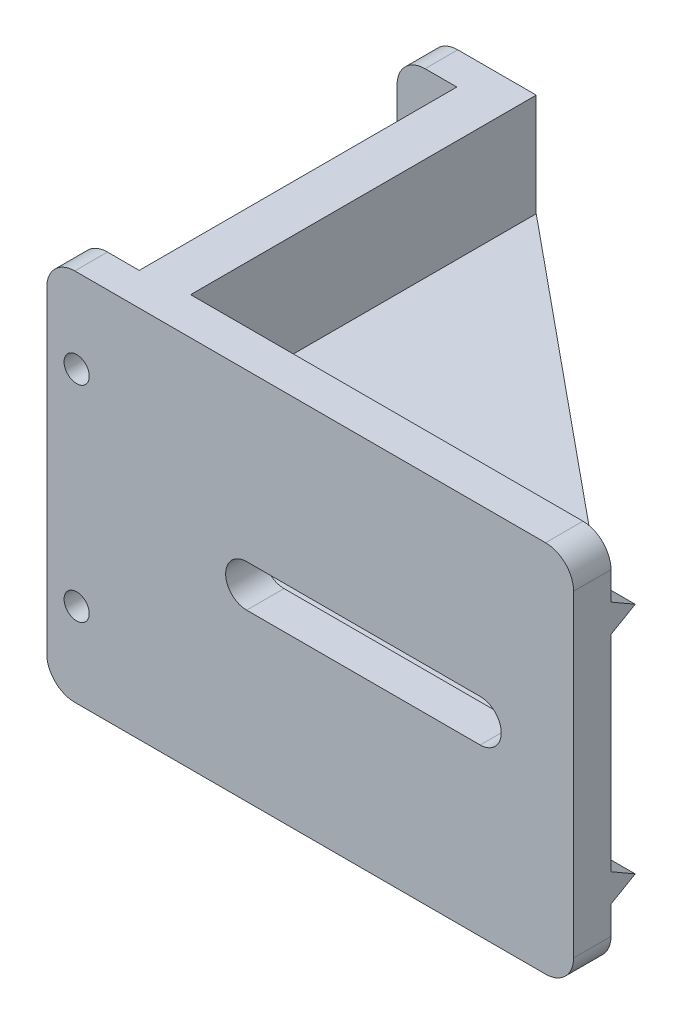
SolidWorks part; units mm, degrees
ref_plane "정면" through (0, 0, 0) normal (0, 0, 1) x (1, 0, 0)
ref_plane "윗면" through (0, 0, 0) normal (0, 1, 0) x (1, 0, 0)
ref_plane "우측면" through (0, 0, 0) normal (1, 0, 0) x (0, 0, -1)
sketch "스케치1" plane through (0, 0, 0) normal (1, 0, 0) x (0, 0, -1)
  line L1 (0, 0) -> (41, 0)
  line L2 (0, 0) -> (0, 40)
  line L3 (0, 40) -> (41, 40)
  line L4 (41, 0) -> (41, 40)
  dimension "D1" = 41
  dimension "D2" = 40
extrude "보스-돌출1" add sketch "스케치1" along normal blind 5
sketch "스케치2" plane through (0, 0, 0) normal (-1, 0, 0) x (0, 0, 1)
  line L0 (-41, 40) -> (0, 40) construction
  line L1 (-3.5, 40) -> (0, 40)
  line L2 (-3.5, 40) -> (-3.5, 0)
  line L3 (-3.5, 0) -> (0, 0)
  line L4 (0, 40) -> (0, 0)
  line L5 (-20.5, -5.7366) -> (-20.5, 42.7612) construction
  line L6 (-37.5, 0) -> (-41, 0)
  line L7 (-41, 40) -> (-41, 0)
  line L8 (-37.5, 40) -> (-41, 40)
  line L9 (-37.5, 40) -> (-37.5, 0)
  dimension "D1" = 3.5
extrude "보스-돌출2" add sketch "스케치2" along normal blind 6.4
sketch "스케치3" plane through (5, 0, 0) normal (1, 0, 0) x (0, 0, -1)
  line L0 (0, 0) -> (41, 0) construction
  line L1 (0, 40) -> (4, 40)
  line L2 (0, 40) -> (0, 0)
  line L3 (0, 0) -> (4, 0)
  line L4 (4, 40) -> (4, 34)
  line L5 (4, 34) -> (6.5981, 32.5)
  line L6 (4, 31) -> (6.5981, 32.5)
  line L7 (-6.5126, 20) -> (43.5218, 20) construction
  line L10 (4, 31) -> (4, 14)
  line L11 (4, 12) -> (4, 9)
  line L12 (4, 14) -> (4, 12)
  line L13 (4, 9) -> (6.5981, 7.5)
  line L14 (4, 6) -> (6.5981, 7.5)
  line L15 (4, 6) -> (4, 0)
  dimension "D1" = 4
  dimension "D2" = 6
  dimension "D3" = 60
  dimension "D4" = 60
  dimension "D5" = 3
  dimension "D6" = 40
extrude "보스-돌출3" add sketch "스케치3" along normal blind 45
sketch "스케치4" plane through (0, 0, -4) normal (0, 0, -1) x (-1, 0, 0)
  line L0 (-50, 9) -> (-50, 31) construction
  line L1 (-50, 29) -> (-5, 29)
  line L2 (-50, 29) -> (-50, 25)
  line L3 (-50, 25) -> (-5, 25)
  line L4 (-5, 29) -> (-5, 25)
  line L5 (-5, 9) -> (-5, 31) construction
  line L8 (-50, 40) -> (-5, 40) construction
  line L10 (-55.9639, 20) -> (9.4654, 20) construction
  line L11 (-50, 15) -> (-5, 15)
  line L12 (-5, 11) -> (-5, 15)
  line L13 (-50, 11) -> (-5, 11)
  line L14 (-50, 11) -> (-50, 15)
  dimension "D1" = 4
  dimension "D2" = 11
extrude "보스-돌출4" add sketch "스케치4" along normal blind 37
sketch "스케치5" plane through (0, 29, 0) normal (0, 1, 0) x (1, 0, 0)
  line L0 (50, 4) -> (5, 41)
  line L1 (5, 41) -> (50, 41)
  line L2 (50, 41) -> (50, 4)
extrude "컷-돌출1" cut sketch "스케치5" against normal blind 19
sketch "스케치6" plane through (0, 0, -41) normal (0, 0, -1) x (-1, 0, 0)
  line L2 (-5, 0) -> (6.4, 0) construction
  line L3 (6.4, 40) -> (6.4, 0) construction
  line L4 (-5, 40) -> (6.4, 40) construction
  circle A1 centre (3.2, 9) radius 1.35
  circle A2 centre (3.2, 31) radius 1.35
  dimension "D1" = 2.7
  dimension "D4" = 2.7
  dimension "D2" = 9
  dimension "D3" = 3.2
  dimension "D5" = 9
extrude "컷-돌출2" cut sketch "스케치6" against normal through all
fillet "필렛1" radius 3 2 edges at (50, 0, -2) (50, 40, -2)
fillet "필렛2" radius 3 4 edges at (-6.4, 0, -1.75) (-6.4, 0, -39.25) (-6.4, 40, -1.75) (-6.4, 40, -39.25)
sketch "스케치7" plane through (0, 0, -4) normal (0, 0, -1) x (-1, 0, 0)
  line L0 (-50, 15) -> (-50, 25) construction
  line L1 (-5, 15) -> (-5, 25) construction
  line L2 (-40, 22.25) -> (-15, 22.25)
  line L3 (-15, 17.75) -> (-40, 17.75)
  arc A0 (-40, 22.25) -> (-40, 17.75) centre (-40, 20) ccw
  arc A1 (-15, 17.75) -> (-15, 22.25) centre (-15, 20) ccw
  dimension "D1" = 4.5
  dimension "D3" = 4.5
  dimension "D2" = 10
  dimension "D4" = 10
extrude "컷-돌출3" cut sketch "스케치7" against normal through all both and the other way through all
